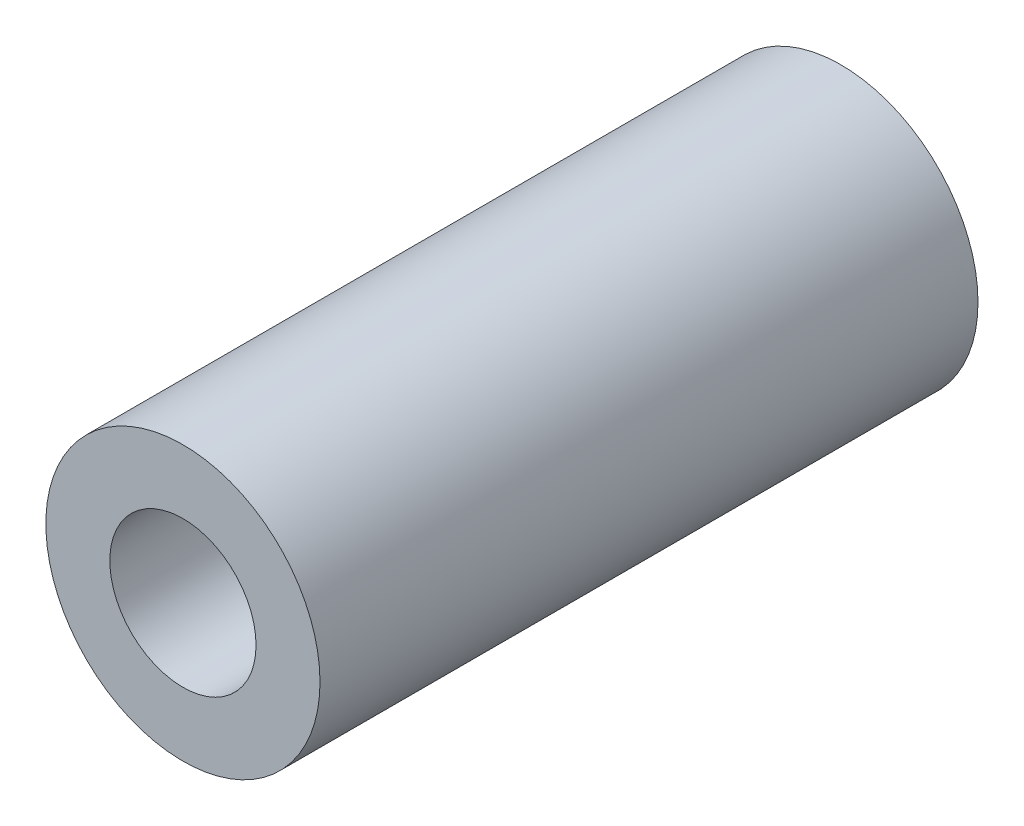
SolidWorks part; units mm, degrees
ref_plane "Front Plane" through (0, 0, 0) normal (0, 0, 1) x (1, 0, 0)
ref_plane "Top Plane" through (0, 0, 0) normal (0, 1, 0) x (1, 0, 0)
ref_plane "Right Plane" through (0, 0, 0) normal (1, 0, 0) x (0, 0, -1)
sketch "Sketch1" plane through (0, 0, 73.3354) normal (0, 0, 1) x (1, 0, 0)
  circle A0 centre (-17.9008, 104.0159) radius 3.75
  circle A1 centre (-17.9008, 104.0159) radius 2
  dimension "D1" = 7.5
extrude "Boss-Extrude1" add sketch "Sketch1" along normal blind 18
